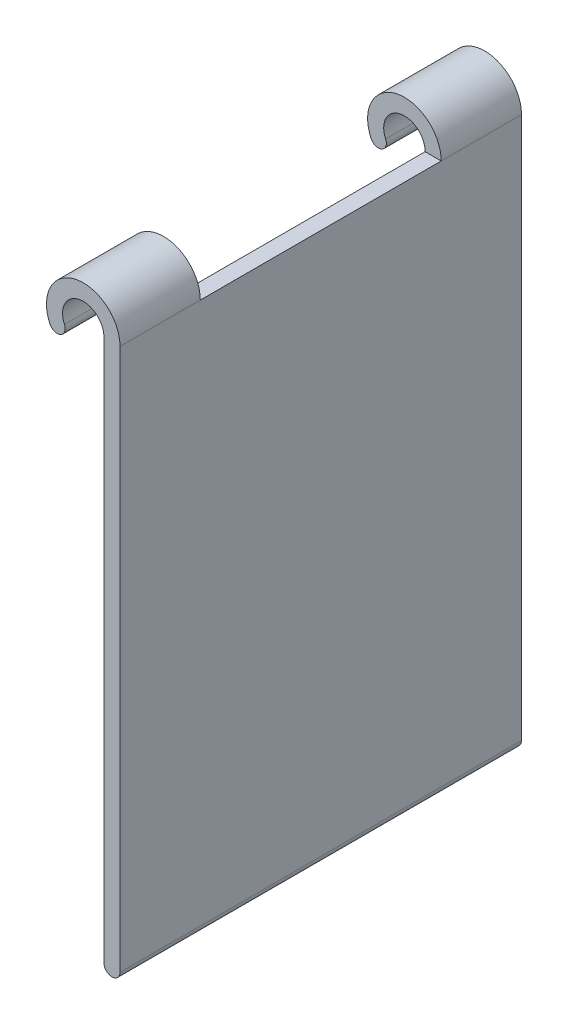
SolidWorks part; units mm, degrees
ref_plane "Front Plane" through (0, 0, 0) normal (0, 0, 1) x (1, 0, 0)
ref_plane "Top Plane" through (0, 0, 0) normal (0, 1, 0) x (1, 0, 0)
ref_plane "Right Plane" through (0, 0, 0) normal (1, 0, 0) x (0, 0, -1)
sketch "Sketch1" plane through (0, 0, 0) normal (0, 0, 1) x (1, 0, 0)
  line L0 (3.2766, 0) -> (3.2766, -85.725)
  line L1 (5.8166, 0) -> (5.8166, -85.725)
  line L2 (-2.9696, -1.3848) -> (-5.2716, -2.4582) construction
  line L3 (0, 0) -> (-9.9121, 0) construction
  line L4 (3.2766, -85.725) -> (5.8166, -85.725) construction
  arc A0 (3.2766, 0) -> (-2.9696, -1.3848) centre (0, 0) ccw construction
  arc A1 (3.2766, 0) -> (-2.9696, -1.3848) centre (0, 0) ccw
  arc A2 (5.8166, 0) -> (-5.2716, -2.4582) centre (0, 0) ccw
  arc A3 (-5.2716, -2.4582) -> (-2.9696, -1.3848) centre (-4.1206, -1.9215) ccw
  arc A4 (3.2766, -85.725) -> (5.8166, -85.725) centre (4.5466, -85.725) ccw
  dimension "D1" = 6.5532
  dimension "D2" = 2.54
  dimension "D5" = 1.27
  dimension "D3" = 25
  dimension "D4" = 85.725
extrude "Boss-Extrude1" add sketch "Sketch1" along normal mid plane 12.7
sketch "Sketch2" plane through (0, 0, 6.35) normal (0, 0, 1) x (1, 0, 0)
  line L5 (3.2766, 0) -> (5.8166, 0)
  line L6 (3.2766, 0) -> (3.2766, -85.725)
  line L8 (5.8166, 0) -> (5.8166, -85.725)
  arc A1 (3.2766, -85.725) -> (5.8166, -85.725) centre (4.5466, -85.725) ccw
extrude "Boss-Extrude2" add sketch "Sketch2" along normal blind 50.8
pattern_linear "LPattern1" count 2 spacing 50.8 along (0, 0, 1) of "Boss-Extrude1"
ref_plane "Plane1" through (0, 0, 25.4) normal (0, 0, 1) x (1, 0, 0)
sketch "Sketch4" plane through (0, 0, 25.4) normal (0, 0, 1) x (1, 0, 0)
  line L1 (0, -66.802) -> (0, -85.6757) construction
  line L2 (5.8166, -85.725) -> (5.8166, 0) construction
  line L3 (3.2766, 0) -> (3.2766, -85.725) construction
  line L4 (-2.8376, -65.1637) -> (-5.0373, -63.8937) construction
  line L5 (3.2766, -66.802) -> (3.2766, -71.6079)
  line L6 (-3.9375, -64.5287) -> (0, -66.802) construction
  line L7 (-5.0373, -63.8937) -> (-2.8376, -65.1637)
  arc A1 (3.2766, 0) -> (-2.9696, -1.3848) centre (0, 0) ccw construction
  arc A2 (-5.0373, -63.8937) -> (3.2766, -71.6079) centre (0, -66.802) ccw
  arc A6 (-2.8376, -65.1637) -> (3.2766, -66.802) centre (0, -66.802) ccw
  dimension "D1" = 120
  dimension "D2" = 66.802
extrude "Boss-Extrude3" add sketch "Sketch4" along normal mid plane 12.7
sketch "Sketch5" plane through (5.8166, 0, 0) normal (1, 0, 0) x (0, 0, -1)
  line L0 (-34.5887, -19.9148) -> (-27.1247, -19.9148) construction
  text T0 "6" font "Circular Std Bold" height 12.7
extrude "Cut-Extrude1" [suppressed] cut sketch "Sketch5" against normal blind 2.54
